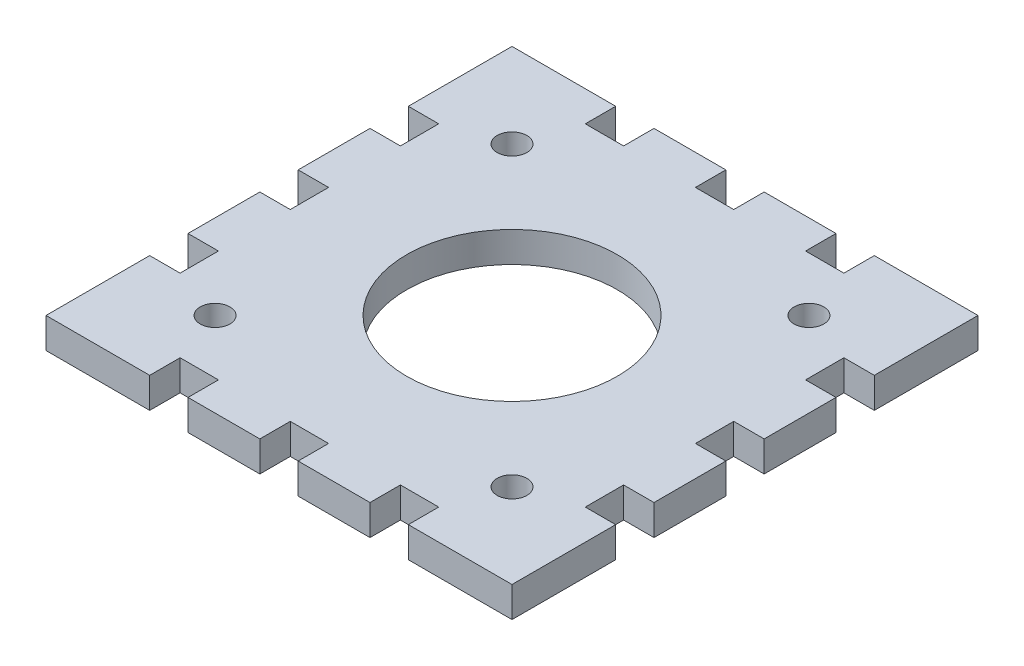
SolidWorks part; units mm, degrees
ref_plane "Front Plane" through (0, 0, 0) normal (0, 0, 1) x (1, 0, 0)
ref_plane "Top Plane" through (0, 0, 0) normal (0, 1, 0) x (1, 0, 0)
ref_plane "Right Plane" through (0, 0, 0) normal (1, 0, 0) x (0, 0, -1)
sketch "Sketch2" plane through (0, 0, 0) normal (0, 1, 0) x (1, 0, 0)
  line L0 (24.325, 9.5) -> (21.15, 9.5)
  line L1 (-24.325, 24.325) -> (24.325, 24.325)
  line L2 (-24.325, 24.325) -> (-24.325, -24.325)
  line L3 (-24.325, -24.325) -> (24.325, -24.325)
  line L4 (24.325, 24.325) -> (24.325, -24.325)
  line L5 (-13.5, 24.325) -> (-9.5, 24.325)
  line L6 (-13.5, 24.325) -> (-13.5, 21.15)
  line L7 (-13.5, 21.15) -> (-9.5, 21.15)
  line L8 (-9.5, 24.325) -> (-9.5, 21.15)
  line L9 (-2, 24.325) -> (2, 24.325)
  line L10 (-2, 24.325) -> (-2, 21.15)
  line L11 (-2, 21.15) -> (2, 21.15)
  line L12 (2, 24.325) -> (2, 21.15)
  line L13 (9.5, 24.325) -> (13.5, 24.325)
  line L14 (9.5, 24.325) -> (9.5, 21.15)
  line L15 (9.5, 21.15) -> (13.5, 21.15)
  line L16 (13.5, 24.325) -> (13.5, 21.15)
  line L17 (24.325, 13.5) -> (21.15, 13.5)
  line L18 (21.15, 13.5) -> (21.15, 9.5)
  line L19 (24.325, 2) -> (21.15, 2)
  line L20 (24.325, -2) -> (21.15, -2)
  line L21 (21.15, 2) -> (21.15, -2)
  line L22 (24.325, -9.5) -> (21.15, -9.5)
  line L23 (24.325, -13.5) -> (21.15, -13.5)
  line L24 (21.15, -9.5) -> (21.15, -13.5)
  line L25 (9.5, -24.325) -> (9.5, -21.15)
  line L26 (13.5, -24.325) -> (13.5, -21.15)
  line L27 (13.5, -21.15) -> (9.5, -21.15)
  line L28 (2, -24.325) -> (2, -21.15)
  line L29 (-2, -24.325) -> (-2, -21.15)
  line L30 (2, -21.15) -> (-2, -21.15)
  line L31 (-9.5, -24.325) -> (-9.5, -21.15)
  line L32 (-13.5, -24.325) -> (-13.5, -21.15)
  line L33 (-9.5, -21.15) -> (-13.5, -21.15)
  line L34 (-24.325, -9.5) -> (-21.15, -9.5)
  line L35 (-24.325, -13.5) -> (-21.15, -13.5)
  line L36 (-21.15, -13.5) -> (-21.15, -9.5)
  line L37 (-24.325, -2) -> (-21.15, -2)
  line L38 (-24.325, 2) -> (-21.15, 2)
  line L39 (-21.15, -2) -> (-21.15, 2)
  line L40 (-24.325, 9.5) -> (-21.15, 9.5)
  line L41 (-24.325, 13.5) -> (-21.15, 13.5)
  line L42 (-21.15, 9.5) -> (-21.15, 13.5)
  circle A0 centre (0, 0) radius 11
  circle A1 centre (-15.5, 15.5) radius 1.55
  circle A2 centre (15.5, 15.5) radius 1.55
  circle A3 centre (15.5, -15.5) radius 1.55
  circle A4 centre (-15.5, -15.5) radius 1.55
  point P4 (0, 24.325)
  point P6 (24.325, 0)
  point P19 (-11.5, 21.15)
  point P59 (0, 0)
  dimension "D13" = 22
  dimension "D14" = 3.1
  dimension "D1" = 48.65
  dimension "D2" = 48.65
  dimension "D3" = 3.175
  dimension "D4" = 3.175
  dimension "D5" = 3.175
  dimension "D6" = 4
  dimension "D7" = 4
  dimension "D8" = 4
  dimension "D9" = 7.5
  dimension "D10" = 7.5
  dimension "D11" = 10.825
  dimension "D15" = 8.825
  dimension "D18" = 8.825
  dimension "D16" = 2
  dimension "D17" = 2
  dimension "D12" = 4
extrude "Boss-Extrude1" add sketch "Sketch2" along normal blind 3.175 contours L42 L40 L2 L38 L39 L37 L34 L36 L35 L3 L32 L33 L31 L29 L30 L28 L25 L27 L26 L4 L23 L24 L22 L20 L21 L19 L0 L18 L17 L1 L16 L15 L14 L12 L11 L10 L8 L7 L6
equation "\"motor width\"=4.865"
equation "\"D1@Sketch2\"=\"motor width\""
equation "\"D2@Sketch2\"=\"motor width\""
equation "\"width\"=0.3175"
equation "\"D3@Sketch2\"=\"width\""
equation "\"D4@Sketch2\"=\"width\""
equation "\"D5@Sketch2\"=\"width\""
equation "\"tooth width\"=0.4"
equation "\"D6@Sketch2\"=\"tooth width\""
equation "\"D7@Sketch2\"=\"tooth width\""
equation "\"D8@Sketch2\"=\"tooth width\""
equation "\"tooth distance\"=0.75"
equation "\"D9@Sketch2\"=\"tooth distance\""
equation "\"D10@Sketch2\"=\"tooth distance\""
equation "\"D11@Sketch2\"=(\"motor width\"-\"tooth distance\"*2-\"tooth width\"*3)/2"
equation "\"D15@Sketch2\"=(\"motor width\"-3.1)/2"
equation "\"D18@Sketch2\"=(\"motor width\"-3.1)/2"
